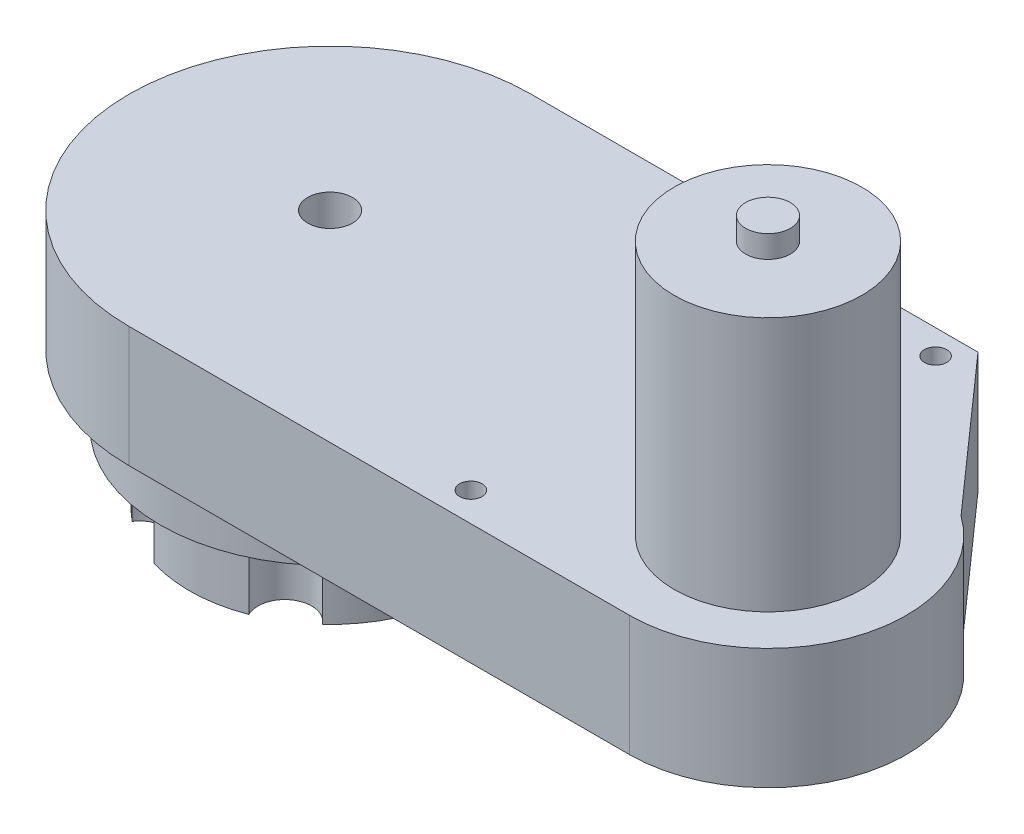
SolidWorks part; units mm, degrees
ref_plane "Front Plane" through (0, 0, 0) normal (0, 0, 1) x (1, 0, 0)
ref_plane "Top Plane" through (0, 0, 0) normal (0, 1, 0) x (1, 0, 0)
ref_plane "Right Plane" through (0, 0, 0) normal (1, 0, 0) x (0, 0, -1)
sketch "Sketch1" plane through (0, 0, 0) normal (0, 1, 0) x (1, 0, 0)
  line L0 (0, 45) -> (100, 45)
  line L1 (100, 45) -> (129.8624, 11.3364)
  line L2 (0, -45) -> (112, -45)
  circle A0 centre (0, 0) radius 45
  circle A1 centre (112, -14) radius 18
  circle A2 centre (112, -14) radius 31
  circle A3 centre (0, 0) radius 5
  circle A4 centre (112, -14) radius 18.5
  circle A5 centre (96, 39.5) radius 2.5
  circle A6 centre (70, -38.5) radius 2.5
  dimension "D2" = 10
  dimension "D3" = 90
  dimension "D4" = 62
  dimension "D5" = 36
  dimension "D6" = 37
  dimension "D7" = 45
  dimension "D9" = 5
  dimension "D12" = 5
  dimension "D1" = 100
  dimension "D8" = 112
  dimension "D10" = 5.5
  dimension "D11" = 96
  dimension "D13" = 70
  dimension "D14" = 6.5
extrude "Boss-Extrude1" add sketch "Sketch1" along normal blind 27 contours A2 L1 L0 A0 L2 A6 A5 | A0 A3 | A2 L1 A4 | A1 | A4 A1
sketch "Sketch2" plane through (0, 27, 0) normal (0, 1, 0) x (1, 0, 0)
  circle A1 centre (112, -14) radius 21
  dimension "D2" = 42
extrude "Boss-Extrude2" add sketch "Sketch2" along normal blind 57 separate body
sketch "Sketch4" plane through (0, 0, 0) normal (0, -1, 0) x (1, 0, 0)
  circle A0 centre (0, 0) radius 38
  circle A1 centre (0, 0) radius 33
  dimension "D1" = 76
  dimension "D2" = 66
extrude "Boss-Extrude3" add sketch "Sketch4" along normal blind 15
sketch "Sketch5" plane through (0, -15, 0) normal (0, -1, 0) x (1, 0, 0)
  line L0 (25.4866, -0.8276) -> (-25.4866, 0.8276) construction
  line L1 (13.46, 21.6582) -> (-13.46, -21.6582) construction
  line L2 (12.0266, -22.4858) -> (-12.0266, 22.4858) construction
  line L3 (12.0266, -22.4858) -> (14.8563, -27.7766) construction
  line L4 (25.4866, -0.8276) -> (31.4834, -1.0223) construction
  line L5 (13.46, 21.6582) -> (16.6271, 26.7543) construction
  arc A0 (31.1061, 4.9658) -> (21.3983, 23.1163) centre (0, 0) ccw
  arc A4 (9.3201, -30.0896) -> (19.8536, -24.4558) centre (14.8563, -27.7766) cw
  arc A5 (-31.1061, -4.9658) -> (-30.7184, 6.9734) centre (-31.4834, 1.0223) ccw
  arc A6 (21.3983, 23.1163) -> (11.2526, 29.4216) centre (16.6271, 26.7543) cw
  arc A7 (30.7184, -6.9734) -> (31.1061, 4.9658) centre (31.4834, -1.0223) cw
  arc A8 (-11.2526, -29.4216) -> (-21.3983, -23.1163) centre (-16.6271, -26.7543) ccw
  arc A9 (-19.8536, 24.4558) -> (-9.3201, 30.0896) centre (-14.8563, 27.7766) ccw
  arc A10 (11.2526, 29.4216) -> (-9.3201, 30.0896) centre (0, 0) ccw
  arc A11 (-19.8536, 24.4558) -> (-30.7184, 6.9734) centre (0, 0) ccw
  arc A12 (-31.1061, -4.9658) -> (-21.3983, -23.1163) centre (0, 0) ccw
  arc A13 (-11.2526, -29.4216) -> (9.3201, -30.0896) centre (0, 0) ccw
  arc A14 (19.8536, -24.4558) -> (30.7184, -6.9734) centre (0, 0) ccw
  arc A15 (20.0203, -21.6665) -> (28.2913, -8.3579) centre (0, 0) ccw
  arc A16 (28.2913, -8.3579) -> (28.7739, 6.5048) centre (31.4834, -1.0223) cw
  arc A17 (28.7739, 6.5048) -> (21.3838, 20.322) centre (0, 0) ccw
  arc A18 (21.3838, 20.322) -> (8.7536, 28.1713) centre (16.6271, 26.7543) cw
  arc A19 (8.7536, 28.1713) -> (-6.9075, 28.6799) centre (0, 0) ccw
  arc A20 (-20.0203, 21.6665) -> (-6.9075, 28.6799) centre (-14.8563, 27.7766) ccw
  arc A21 (-20.0203, 21.6665) -> (-28.2913, 8.3579) centre (0, 0) ccw
  arc A22 (-28.7739, -6.5048) -> (-28.2913, 8.3579) centre (-31.4834, 1.0223) ccw
  arc A23 (-28.7739, -6.5048) -> (-21.3838, -20.322) centre (0, 0) ccw
  arc A24 (-8.7536, -28.1713) -> (-21.3838, -20.322) centre (-16.6271, -26.7543) ccw
  arc A25 (-8.7536, -28.1713) -> (6.9075, -28.6799) centre (0, 0) ccw
  arc A26 (6.9075, -28.6799) -> (20.0203, -21.6665) centre (14.8563, -27.7766) cw
  dimension "D3" = 120
  dimension "D4" = 60
  dimension "D6" = 2
extrude "Boss-Extrude4" add sketch "Sketch5" along normal blind 16 and the other way up to surface (15 mm away) other way up to face at (0, 0, 38)
sketch "Sketch6" plane through (0, 84, 0) normal (0, 1, 0) x (1, 0, 0)
  circle A0 centre (112, -14) radius 5
  dimension "D1" = 10
extrude "Boss-Extrude5" add sketch "Sketch6" along normal blind 5
sketch "Sketch7" plane through (0, 0, 0) normal (0, -1, 0) x (1, 0, 0)
  circle A0 centre (0, 0) radius 33
  dimension "D1" = 66
extrude "Boss-Extrude6" add sketch "Sketch7" along normal blind 15
sketch "Sketch8" plane through (0, 27, 0) normal (0, 1, 0) x (1, 0, 0)
  circle A0 centre (0, 0) radius 5 construction
  circle A1 centre (0, 0) radius 5
extrude "Cut-Extrude1" cut sketch "Sketch8" against normal blind 87
sketch "Sketch9" plane through (0, 27, 0) normal (0, 1, 0) x (1, 0, 0)
  line L3 (0, -45) -> (112, -45)
  line L4 (129.8624, 11.3364) -> (100, 45)
  line L5 (100, 45) -> (0, 45)
  line L6 (0, -45) -> (112, -45)
  line L7 (129.8624, 11.3364) -> (100, 45)
  line L8 (100, 45) -> (0, 45)
  arc A2 (112, -45) -> (129.8624, 11.3364) centre (112, -14) ccw
  arc A3 (0, 45) -> (0, -45) centre (0, 0) ccw
  arc A4 (112, -45) -> (129.8624, 11.3364) centre (112, -14) ccw
  arc A5 (0, 45) -> (0, -45) centre (0, 0) ccw
  point P2 (96, 39.5)
  dimension "D1" = 0
ref_plane "Plane1" through (96, 0, 0) normal (1, 0, 0) x (0, 0, -1)
sketch "Sketch10" plane through (96, 0, 0) normal (1, 0, 0) x (0, 0, -1)
  line L0 (39.5, 27) -> (39.5, 37) construction
  dimension "D1" = 10
